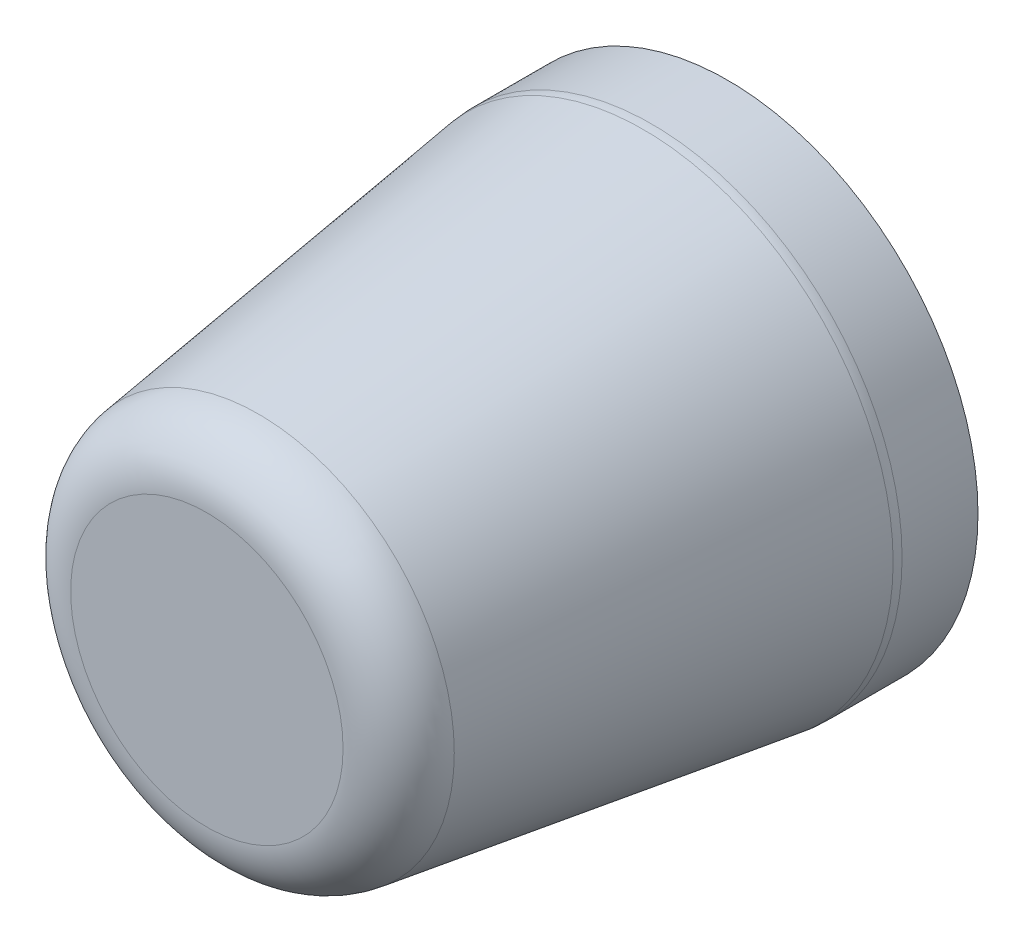
SolidWorks part; units mm, degrees
ref_plane "Front Plane" through (0, 0, 0) normal (0, 0, 1) x (1, 0, 0)
ref_plane "Top Plane" through (0, 0, 0) normal (0, 1, 0) x (1, 0, 0)
ref_plane "Right Plane" through (0, 0, 0) normal (1, 0, 0) x (0, 0, -1)
sketch "Sketch1" plane through (0, 0, 0) normal (1, 0, 0) x (0, 0, -1)
  line L0 (0, 0) -> (-14.411, 0) construction
  line L1 (-26, 0) -> (-15, 0)
  line L2 (-15, 0) -> (-15, 2)
  line L3 (-15, 2) -> (0, 2)
  line L4 (0, 2) -> (0, 12.5)
  line L5 (0, 12.5) -> (-4, 12.5)
  line L6 (-4, 12.5) -> (-26, 9.4081)
  line L7 (-26, 9.4081) -> (-26, 0)
  dimension "D1" = 4
  dimension "D2" = 15
  dimension "D3" = 25
  dimension "D4" = 26
  dimension "D5" = 8
  dimension "D6" = 4
revolve "Revolve1" add sketch "Sketch1" angle 360 about L0
fillet "Fillet1" radius 3 2 edges at (-9.4081, 0, 26) (-12.5, 0, 4)
